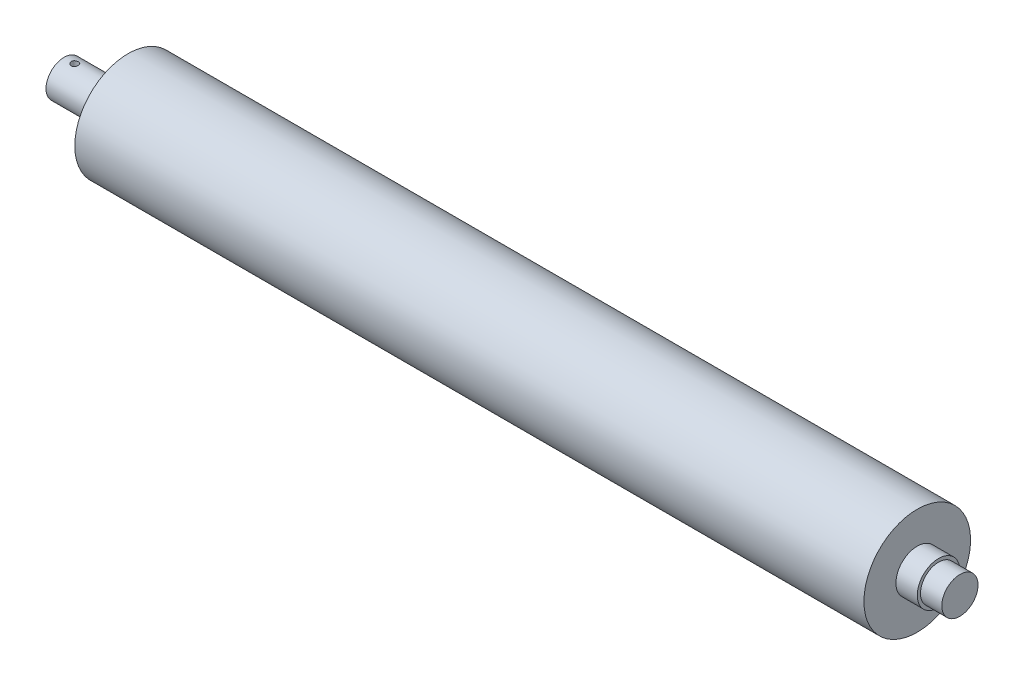
SolidWorks part; units mm, degrees
ref_plane "前视基准面" through (0, 0, 0) normal (0, 0, 1) x (1, 0, 0)
ref_plane "上视基准面" through (0, 0, 0) normal (0, 1, 0) x (1, 0, 0)
ref_plane "右视基准面" through (0, 0, 0) normal (1, 0, 0) x (0, 0, -1)
sketch "草图2" plane through (0, 0, 0) normal (0, 0, 1) x (1, 0, 0)
  line L0 (-62.7059, 0) -> (66, 0) construction
  line L3 (354.5079, 10) -> (344.5079, 10)
  line L4 (344.5079, 10) -> (344.5079, 25)
  line L5 (344.5079, 25) -> (-25.4921, 25)
  line L6 (-25.4921, 25) -> (-25.4921, 10)
  line L7 (-25.4921, 10) -> (-35.4921, 10)
  line L8 (-35.4921, 10) -> (-35.4921, 8.5)
  line L9 (-35.4921, 8.5) -> (-45.4921, 8.5)
  line L11 (354.5079, 10) -> (354.5079, 8.5)
  line L12 (354.5079, 8.5) -> (364.5079, 8.5)
  line L14 (-39.7938, 0) -> (364.5079, 0)
  line L18 (159.5079, 96.5403) -> (159.5079, -92.5436) construction
  line L19 (364.5079, 8.5) -> (364.5079, 0)
  line L20 (-45.4921, 8.5) -> (-55.4921, 8.5)
  line L21 (-55.4921, 8.5) -> (-55.4921, 0)
  line L22 (-55.4921, 0) -> (-39.7938, 0)
  dimension "D2" = 10
  dimension "D3" = 10
  dimension "D4" = 370
  dimension "D5" = 25
  dimension "D6" = 10
  dimension "D8" = 10
  dimension "D9" = 8.5
revolve "旋转1" add sketch "草图2" angle 360 about L0
ref_plane "基准面1" through (159.5079, 0, 0) normal (-1, 0, 0) x (0, 0, 1)
sketch "草图3" plane through (-55.4921, 0, 0) normal (-1, 0, 0) x (0, 0, 1)
  circle A0 centre (0, 0) radius 6.05
  dimension "D1" = 12.1
ref_plane "基准面2" through (0, 8.5, 0) normal (0, 1, 0) x (1, 0, 0)
sketch "草图4" plane through (0, 8.5, 0) normal (0, 1, 0) x (1, 0, 0)
  line L0 (-117.1309, 0) -> (51.2961, 0) construction
  line L1 (-35.4921, 10) -> (-35.4921, -10) construction
  circle A0 centre (-50.4921, 0) radius 2
  dimension "D1" = 4
  dimension "D2" = 15
hole_wizard "M4 螺纹孔1" positions "草图5" profile "草图6" tap size "M4" standard "GB"
sketch "草图5" plane through (0, 8.5, 0) normal (0, 1, 0) x (1, 0, 0)
  point P0 (-50.4921, 0)
sketch "草图6" plane through (-50.4921, 8.5, 0) normal (1, 0, 0) x (0, 0, 1)
  line L0 (0, 0) -> (0, 20.9914)
  line L1 (0, 20.9914) -> (1.65, 20)
  line L2 (1.65, 20) -> (1.65, 0)
  line L5 (1.65, 0) -> (0, 0)
  line L10 (0, 20.9914) -> (-1.65, 20) construction
  line L11 (0, -6.35) -> (0, 107.95) construction
  dimension "螺纹孔钻头直径" = 3.3
  dimension "螺纹孔钻头深度" = 20
  dimension "导头角度" = 118
cosmetic thread "孔螺蚊线1" parameters "D1"=8, "D2"=4
hole_wizard "大小mm Clearance 暗销孔1" positions "草图7" profile "草图8" hole size "Ø12.0" standard "GB"
sketch "草图7" plane through (-55.4921, 0, 0) normal (-1, 0, 0) x (0, 0, 1)
  point P0 (0, 0)
sketch "草图8" plane through (-55.4921, 0, 0) normal (0, 1, 0) x (0, 0, 1)
  line L0 (0, 0) -> (0, 15.6352)
  line L1 (0, 15.6352) -> (6.05, 12)
  line L2 (6.05, 12) -> (6.05, 0)
  line L5 (6.05, 0) -> (0, 0)
  line L10 (0, 15.6352) -> (-6.05, 12) construction
  line L11 (0, -6.35) -> (0, 107.95) construction
  dimension "孔直径" = 12.1
  dimension "孔深度" = 12
  dimension "导头角度" = 118
